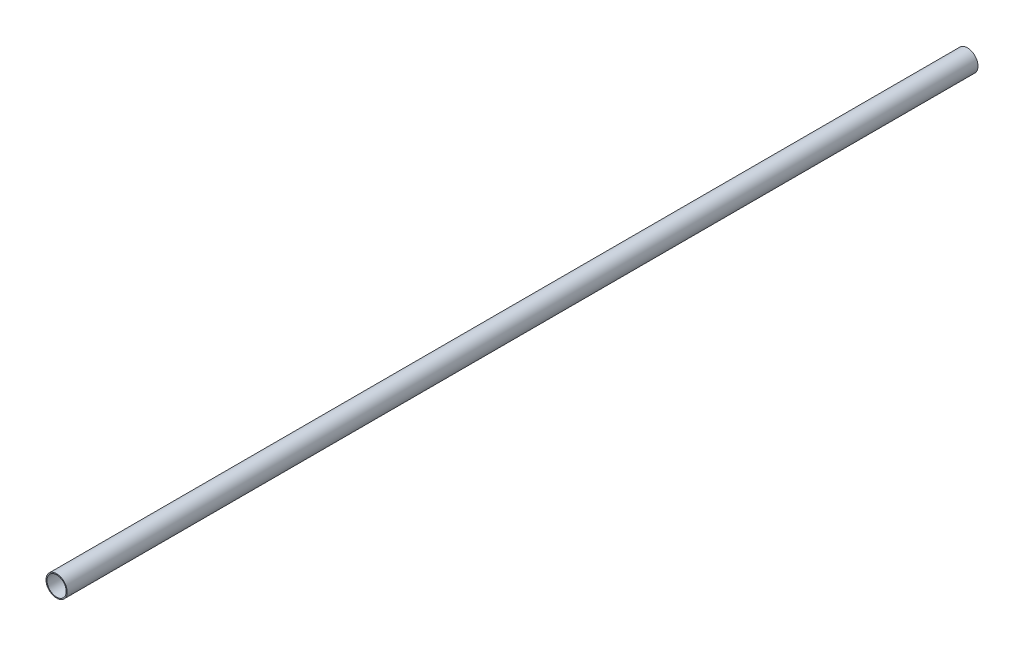
SolidWorks part; units mm, degrees
material "Carbon Fiber Tube - UD Approx"
ref_plane "Front Plane" through (0, 0, 0) normal (0, 0, 1) x (1, 0, 0)
ref_plane "Top Plane" through (0, 0, 0) normal (0, 1, 0) x (1, 0, 0)
ref_plane "Right Plane" through (0, 0, 0) normal (1, 0, 0) x (0, 0, -1)
sketch "Sketch1" plane through (0, 0, 0) normal (0, 0, 1) x (1, 0, 0)
  circle A0 centre (0, 0) radius 11
  circle A1 centre (0, 0) radius 10
  dimension "D1" = 22
  dimension "D2" = 20
extrude "Boss-Extrude1" add sketch "Sketch1" along normal blind 944
